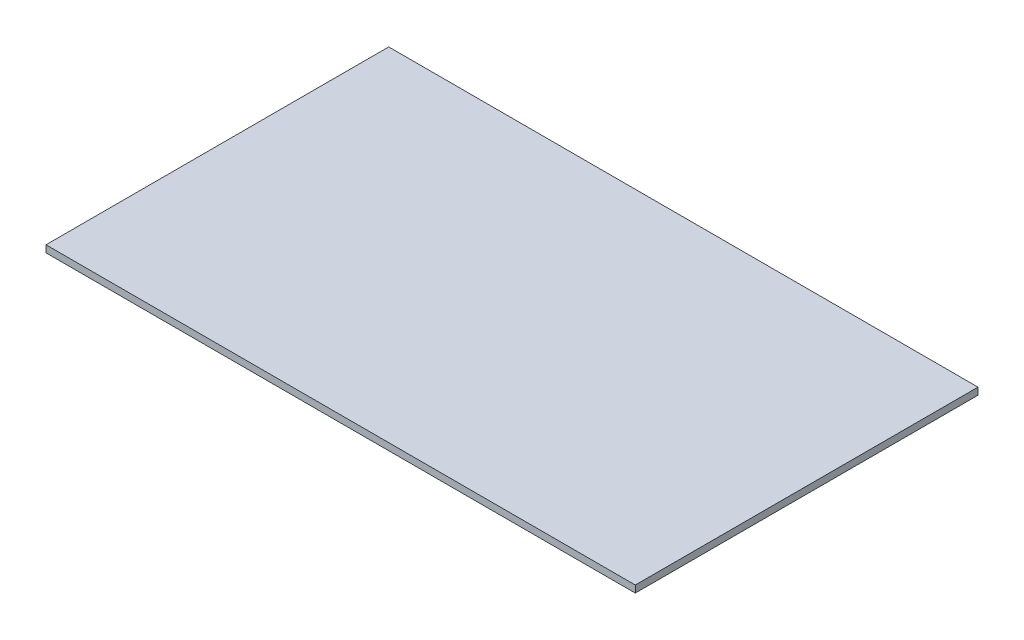
SolidWorks part; units mm, degrees
ref_plane "Front Plane" through (0, 0, 0) normal (0, 0, 1) x (1, 0, 0)
ref_plane "Top Plane" through (0, 0, 0) normal (0, 1, 0) x (1, 0, 0)
ref_plane "Right Plane" through (0, 0, 0) normal (1, 0, 0) x (0, 0, -1)
sketch "Sketch1" plane through (0, 0, 0) normal (0, 1, 0) x (1, 0, 0)
  line L1 (-146.3128, -73.583) -> (106.0021, -73.583)
  line L2 (-146.3128, -73.583) -> (-146.3128, 73.1564)
  line L3 (-146.3128, 73.1564) -> (106.0021, 73.1564)
  line L4 (106.0021, -73.583) -> (106.0021, 73.1564)
extrude "Boss-Extrude1" add sketch "Sketch1" along normal blind 3
